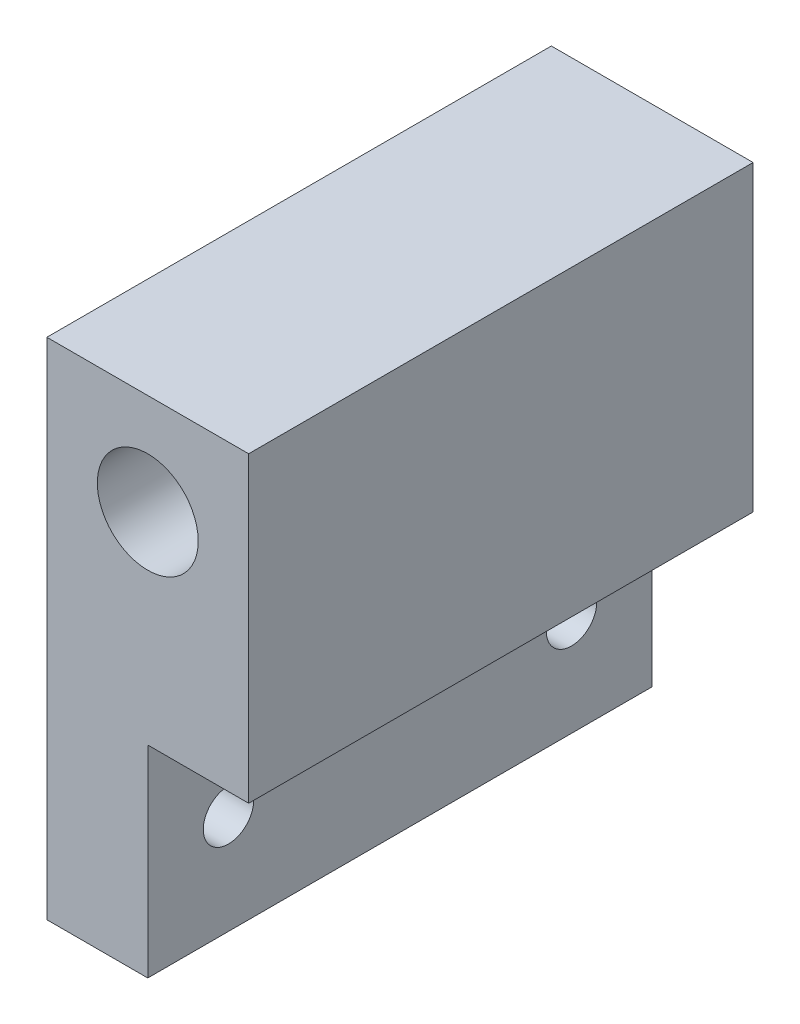
SolidWorks part; units mm, degrees
ref_plane "Plan de face" through (0, 0, 0) normal (0, 0, 1) x (1, 0, 0)
ref_plane "Plan de dessus" through (0, 0, 0) normal (0, 1, 0) x (1, 0, 0)
ref_plane "Plan de droite" through (0, 0, 0) normal (1, 0, 0) x (0, 0, -1)
sketch "Esquisse1" plane through (0, 0, 0) normal (0, 0, 1) x (1, 0, 0)
  line L0 (0, 0) -> (0, 16.1141) construction
  line L1 (-10, 10) -> (10, 10)
  line L2 (-10, 10) -> (-10, -10)
  line L3 (-10, -10) -> (10, -10)
  line L4 (10, 10) -> (10, -10)
  line L5 (0, 16.1141) -> (0, 0) construction
  line L6 (0, 0) -> (18.9044, 0) construction
  line L8 (-10, -10) -> (10, -10)
  line L9 (-10, -10) -> (-10, -40)
  line L10 (-10, -40) -> (10, -40)
  line L11 (10, -10) -> (10, -40)
  line L12 (0, 0) -> (0, -21.5549) construction
  circle A0 centre (0, 0) radius 5
  dimension "D1" = 10
  dimension "D2" = 20
  dimension "D3" = 30
  dimension "D4" = 20
extrude "Boss.-Extru.1" add sketch "Esquisse1" along normal blind 15 contours L4 L1 L2 L3 A0 | L11 L3 L9 L10
sketch "Esquisse2" plane through (0, 0, 15) normal (0, 0, 1) x (1, 0, 0)
  line L0 (10, 10) -> (10, -40) construction
  line L1 (-10, 10) -> (10, 10)
  line L2 (-10, 10) -> (-10, -40)
  line L3 (-10, -40) -> (10, -40)
  line L4 (10, 10) -> (10, -40)
  line L5 (-10, -40) -> (10, -40) construction
  circle A0 centre (0, 0) radius 5
extrude "Boss.-Extru.2" add sketch "Esquisse2" along normal blind 35
sketch "Esquisse3" plane through (10, 0, 0) normal (1, 0, 0) x (0, 0, -1)
  line L0 (-50, -40) -> (0, -40) construction
  line L1 (0, 10) -> (0, -40) construction
  line L2 (-50, -40) -> (-50, 10) construction
  circle A0 centre (-42, -30) radius 2.5
  circle A1 centre (-8, -30) radius 2.5
  dimension "D1" = 5
  dimension "D2" = 5
  dimension "D3" = 10
  dimension "D4" = 10
  dimension "D5" = 8
  dimension "D6" = 8
extrude "Enlèv. mat.-Extru.1" cut sketch "Esquisse3" against normal blind 30
sketch "Esquisse4" plane through (10, 0, 0) normal (1, 0, 0) x (0, 0, -1)
  line L0 (0, 10) -> (0, -40) construction
  line L1 (-50, -40) -> (0, -40)
  line L2 (-50, -40) -> (-50, -20)
  line L3 (-50, -20) -> (0, -20)
  line L4 (0, -40) -> (0, -20)
  dimension "D1" = 20
extrude "Enlèv. mat.-Extru.2" cut sketch "Esquisse4" against normal blind 10
